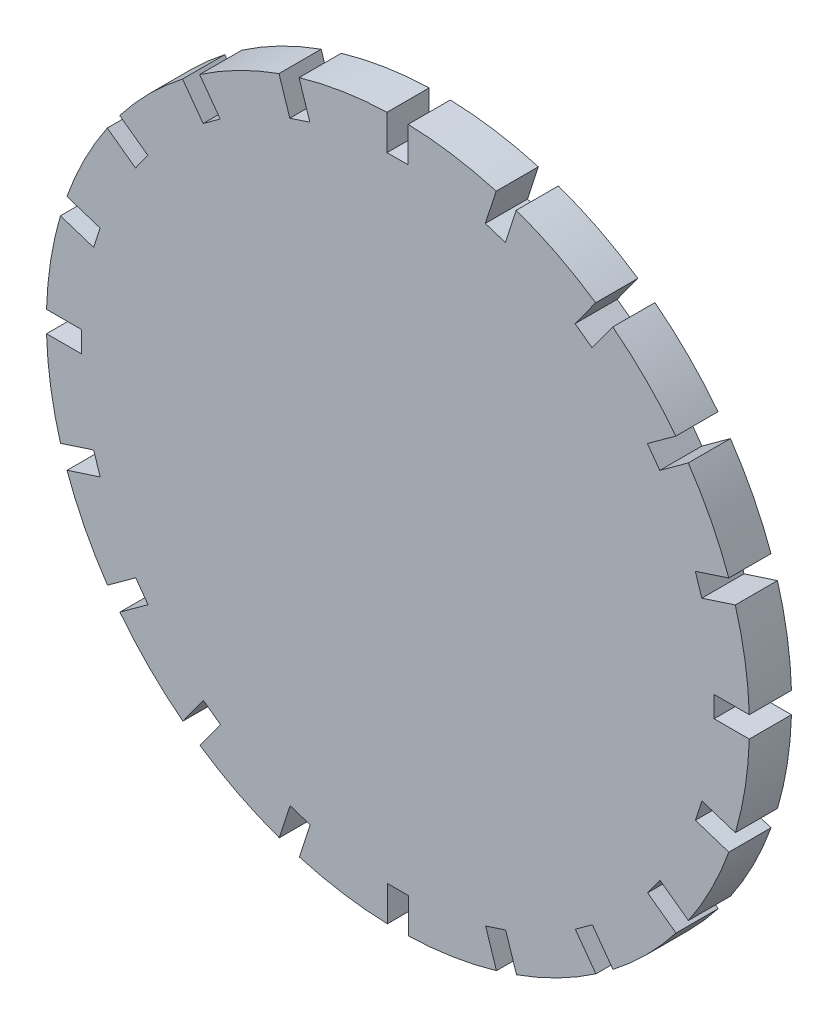
SolidWorks part; units mm, degrees
ref_plane "Front Plane" through (0, 0, 0) normal (0, 0, 1) x (1, 0, 0)
ref_plane "Top Plane" through (0, 0, 0) normal (0, 1, 0) x (1, 0, 0)
ref_plane "Right Plane" through (0, 0, 0) normal (1, 0, 0) x (0, 0, -1)
sketch "Sketch2" plane through (0, 0, 0) normal (0, 0, 1) x (1, 0, 0)
  line L0 (-155.1279, 0) -> (168.9897, -1.4796) construction
  line L1 (0, 103.9637) -> (0, -102.4062) construction
  line L2 (-1.5, -50.6857) -> (-1.5, -45.7082)
  line L3 (-1.5, -45.7082) -> (1.5, -45.7082)
  line L4 (1.5, -45.7082) -> (1.5, -50.6857)
  line L5 (-16.8703, -47.7835) -> (-15.3322, -43.0496)
  line L6 (-8, -28.7082) -> (8, -28.7082)
  line L7 (-8, -28.7082) -> (-8, -34.7082)
  line L8 (-8, -34.7082) -> (8, -34.7082)
  line L9 (8, -28.7082) -> (8, -34.7082)
  line L10 (-15.3322, -43.0496) -> (-12.479, -43.9767)
  line L11 (-12.479, -43.9767) -> (-14.0171, -48.7106)
  line L12 (-30.5915, -40.2737) -> (-27.6658, -36.2468)
  line L13 (-27.6658, -36.2468) -> (-25.2388, -38.0102)
  line L14 (-25.2388, -38.0102) -> (-28.1645, -42.037)
  line L15 (-41.3205, -28.8913) -> (-37.2937, -25.9656)
  line L16 (-37.2937, -25.9656) -> (-35.5303, -28.3927)
  line L17 (-35.5303, -28.3927) -> (-39.5572, -31.3184)
  line L18 (-48.0071, -14.7506) -> (-43.2732, -13.2125)
  line L19 (-43.2732, -13.2125) -> (-42.3462, -16.0657)
  line L20 (-42.3462, -16.0657) -> (-47.08, -17.6038)
  line L21 (-49.9967, 0.7642) -> (-45.0192, 0.7642)
  line L22 (-45.0192, 0.7642) -> (-45.0192, -2.2358)
  line L23 (-45.0192, -2.2358) -> (-49.9967, -2.2358)
  line L24 (-47.0945, 16.1345) -> (-42.3606, 14.5964)
  line L25 (-42.3606, 14.5964) -> (-43.2877, 11.7432)
  line L26 (-43.2877, 11.7432) -> (-48.0215, 13.2814)
  line L27 (-39.5847, 29.8558) -> (-35.5578, 26.9301)
  line L28 (-35.5578, 26.9301) -> (-37.3211, 24.503)
  line L29 (-37.3211, 24.503) -> (-41.348, 27.4287)
  line L30 (-28.2023, 40.5848) -> (-25.2766, 36.5579)
  line L31 (-25.2766, 36.5579) -> (-27.7037, 34.7945)
  line L32 (-27.7037, 34.7945) -> (-30.6294, 38.8214)
  line L33 (-14.0616, 47.2713) -> (-12.5235, 42.5374)
  line L34 (-12.5235, 42.5374) -> (-15.3767, 41.6104)
  line L35 (-15.3767, 41.6104) -> (-16.9148, 46.3443)
  line L36 (1.4532, 49.2707) -> (1.4532, 44.2834)
  line L37 (1.4532, 44.2834) -> (-1.5468, 44.2834)
  line L38 (-1.5468, 44.2834) -> (-1.5468, 49.2609)
  line L39 (16.8287, 46.3747) -> (15.2854, 41.6248)
  line L40 (15.2854, 41.6248) -> (12.4323, 42.5519)
  line L41 (12.4323, 42.5519) -> (13.9748, 47.2992)
  line L42 (30.558, 38.8671) -> (27.6191, 34.822)
  line L43 (27.6191, 34.822) -> (25.192, 36.5854)
  line L44 (25.192, 36.5854) -> (28.1296, 40.6286)
  line L45 (41.2953, 27.4822) -> (37.2469, 24.5408)
  line L46 (37.2469, 24.5408) -> (35.4836, 26.9679)
  line L47 (35.4836, 26.9679) -> (39.5303, 29.908)
  line L48 (47.9875, 13.3347) -> (43.2264, 11.7877)
  line L49 (43.2264, 11.7877) -> (42.2994, 14.6409)
  line L50 (42.2994, 14.6409) -> (47.0589, 16.1873)
  line L51 (49.9781, -2.189) -> (44.9724, -2.189)
  line L52 (44.9724, -2.189) -> (44.9724, 0.811)
  line L53 (44.9724, 0.811) -> (49.9769, 0.811)
  line L54 (47.072, -17.5672) -> (42.3138, -16.0212)
  line L55 (42.3138, -16.0212) -> (43.2409, -13.168)
  line L56 (43.2409, -13.168) -> (47.9984, -14.7138)
  line L57 (39.5548, -31.2928) -> (35.511, -28.3549)
  line L58 (35.511, -28.3549) -> (37.2744, -25.9278)
  line L59 (37.2744, -25.9278) -> (41.3178, -28.8655)
  line L60 (28.1641, -42.0214) -> (25.2299, -37.9827)
  line L61 (25.2299, -37.9827) -> (27.6569, -36.2193)
  line L62 (27.6569, -36.2193) -> (30.5911, -40.2579)
  line L63 (14.0172, -48.7032) -> (12.4767, -43.9622)
  line L64 (12.4767, -43.9622) -> (15.3299, -43.0352)
  line L65 (15.3299, -43.0352) -> (16.8703, -47.7761)
  arc A0 (1.5, -50.6857) -> (14.0172, -48.7032) centre (0, -0.7082) ccw
  circle A1 centre (-17.5, -8.7082) radius 2.75
  circle A2 centre (-17.5, -8.7082) radius 5.25
  circle A3 centre (17.5, -8.7082) radius 5.25
  circle A4 centre (17.5, -8.7082) radius 2.75
  arc A5 (-30.625, 38.8154) -> (-39.5758, 29.8493) centre (0, -0.7082) ccw
  arc A6 (-16.9147, 46.3439) -> (-28.1995, 40.5809) centre (0, -0.7082) ccw
  arc A7 (-14.015, -48.7038) -> (-1.5, -50.6857) centre (0, -0.7082) ccw
  arc A8 (-28.1568, -42.0264) -> (-16.8682, -47.7769) centre (0, -0.7082) ccw
  arc A9 (-39.543, -31.3081) -> (-30.5841, -40.2634) centre (0, -0.7082) ccw
  arc A10 (-47.0611, -17.5977) -> (-41.307, -28.8815) centre (0, -0.7082) ccw
  arc A11 (-49.9767, -2.2358) -> (-47.9893, -14.7449) centre (0, -0.7082) ccw
  arc A12 (-48.0046, 13.2759) -> (-49.9783, 0.7642) centre (0, -0.7082) ccw
  arc A13 (-41.3371, 27.4208) -> (-47.0796, 16.1297) centre (0, -0.7082) ccw
  arc A14 (16.8703, -47.7761) -> (28.1641, -42.0214) centre (0, -0.7082) ccw
  arc A15 (30.5911, -40.2579) -> (39.5548, -31.2928) centre (0, -0.7082) ccw
  arc A16 (41.3178, -28.8655) -> (47.072, -17.5672) centre (0, -0.7082) ccw
  arc A17 (47.9984, -14.7138) -> (49.9781, -2.189) centre (0, -0.7082) ccw
  arc A18 (49.9769, 0.811) -> (47.9875, 13.3347) centre (0, -0.7082) ccw
  arc A19 (47.0589, 16.1873) -> (41.2953, 27.4822) centre (0, -0.7082) ccw
  arc A20 (13.9748, 47.2992) -> (1.4532, 49.2707) centre (0, -0.7082) ccw
  arc A21 (28.1296, 40.6286) -> (16.8287, 46.3747) centre (0, -0.7082) ccw
  arc A22 (39.5303, 29.908) -> (30.558, 38.8671) centre (0, -0.7082) ccw
  arc A23 (-1.5468, 49.2609) -> (-14.0602, 47.2669) centre (0, -0.7082) ccw
  point P5 (0, -0.7082)
  point P18 (0, -8.7082)
  point P101 (-0.0234, -0.7124)
  dimension "D1" = 100
  dimension "D3" = 5.5
  dimension "D10" = 10.5
  dimension "D2" = 8.0798
  dimension "D4" = 17.5
  dimension "D5" = 1.5
  dimension "D6" = 20
  dimension "D7" = 16
  dimension "D8" = 8
  dimension "D9" = 6
  dimension "D11" = 3
  dimension "D12" = 45
  dimension "D13" = 20
extrude "Boss-Extrude1" add sketch "Sketch2" along normal blind 6 contours A1 | A3 A4 | L38 A23 L33 L34 L35 A6 L30 L31 L32 A5 L27 L28 L29 A13 L24 L25 L26 A12 L21 L22 L23 A11 L18 L19 L20 A10 L15 L16 L17 A9 L12 L13 L14 A8 L5 L10 L11 A7 L2 L3 L4 A0 L63 L64 L65 A14 L60 L61 L62 A15 L57 | A2 A1
sketch "Sketch4" plane through (0, 0, 0) normal (0, 0, -1) x (-1, 0, 0)
  line L0 (8, -28.7082) -> (8, -34.7082) construction
  line L1 (8, -34.7082) -> (-8, -34.7082) construction
  line L2 (-8, -28.7082) -> (-8, -34.7082) construction
  line L3 (8, -28.7082) -> (-8, -28.7082) construction
  line L4 (8, -28.7082) -> (8, -34.7082)
  line L5 (8, -34.7082) -> (-8, -34.7082)
  line L6 (-8, -28.7082) -> (-8, -34.7082)
  line L7 (8, -28.7082) -> (-8, -28.7082)
  circle A0 centre (17.5, -8.7082) radius 2.75 construction
  circle A1 centre (-17.5, -8.7082) radius 2.75 construction
  circle A2 centre (17.5, -8.7082) radius 2.75
  circle A3 centre (-17.5, -8.7082) radius 2.75
extrude "Boss-Extrude2" add sketch "Sketch4" against normal blind 6
